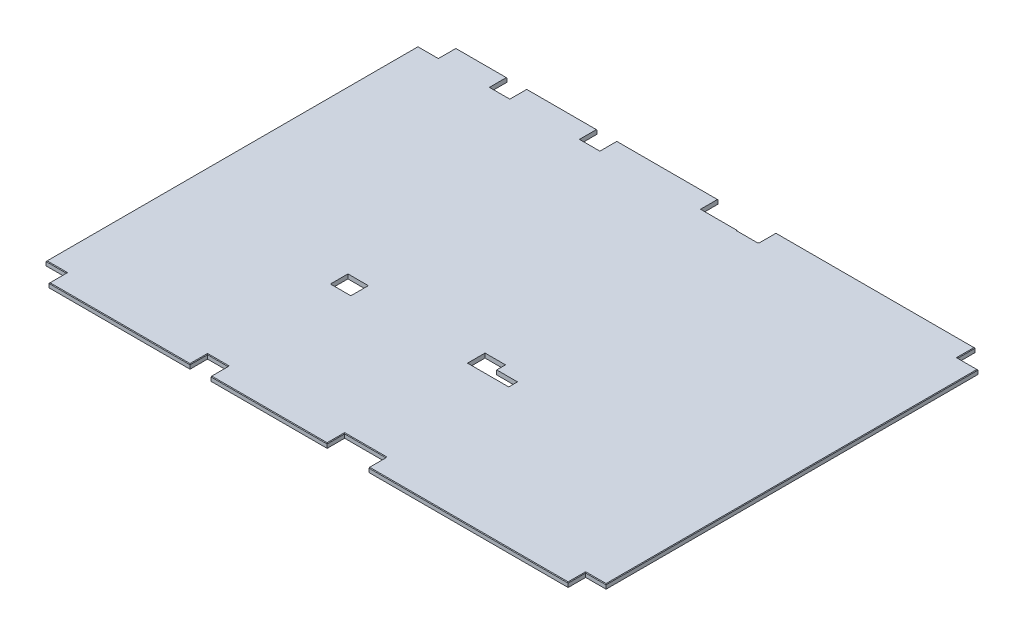
SolidWorks part; units mm, degrees
material "Oak"
ref_plane "Front Plane" through (0, 0, 0) normal (0, 0, 1) x (1, 0, 0)
ref_plane "Top Plane" through (0, 0, 0) normal (0, 1, 0) x (1, 0, 0)
ref_plane "Right Plane" through (0, 0, 0) normal (1, 0, 0) x (0, 0, -1)
sketch "Sketch1" plane through (0, 0, 0) normal (0, 1, 0) x (1, 0, 0)
  line L1 (0, 1771.65) -> (2438.4, 1771.65)
  line L2 (0, 1771.65) -> (0, 0)
  line L3 (0, 0) -> (2438.4, 0)
  line L4 (2438.4, 1771.65) -> (2438.4, 0)
  dimension "D1" = 1771.65
  dimension "D2" = 2438.4
extrude "Boss-Extrude1" add sketch "Sketch1" along normal mid plane 19.05
sketch "Sketch2" plane through (0, 9.525, 0) normal (0, 1, 0) x (1, 0, 0)
  line L0 (0, 0) -> (2438.4, 0) construction
  line L5 (2438.4, 1771.65) -> (0, 1771.65) construction
  line L6 (1390.6627, 1771.65) -> (1479.5627, 1771.65)
  line L7 (0, 1771.65) -> (88.9, 1771.65)
  line L8 (0, 1771.65) -> (0, 1695.45)
  line L9 (0, 1695.45) -> (88.9, 1695.45)
  line L10 (88.9, 1771.65) -> (88.9, 1695.45)
  line L15 (2438.4, 0) -> (2438.4, 1771.65) construction
  line L24 (2349.5, 1771.65) -> (2438.4, 1771.65)
  line L25 (2349.5, 1771.65) -> (2349.5, 1695.45)
  line L26 (2349.5, 1695.45) -> (2438.4, 1695.45)
  line L27 (2438.4, 1771.65) -> (2438.4, 1695.45)
  line L29 (0, 1771.65) -> (0, 0) construction
  line L32 (0, 885.825) -> (2438.4, 885.825) construction
  line L33 (1300.1752, 0) -> (1300.1752, 76.2)
  line L34 (1477.9752, 0) -> (1300.1752, 0)
  line L35 (792.1752, 0) -> (792.1752, 76.2)
  line L36 (2438.4, 0) -> (2438.4, 76.2)
  line L37 (2349.5, 76.2) -> (2438.4, 76.2)
  line L38 (2349.5, 0) -> (2349.5, 76.2)
  line L39 (2349.5, 0) -> (2438.4, 0)
  line L44 (1477.9752, 0) -> (1477.9752, 76.2)
  line L45 (1300.1752, 76.2) -> (1477.9752, 76.2)
  line L46 (703.2752, 76.2) -> (792.1752, 76.2)
  line L47 (703.2752, 0) -> (703.2752, 76.2)
  line L48 (703.2752, 0) -> (792.1752, 0)
  line L49 (88.9, 0) -> (88.9, 76.2)
  line L50 (0, 76.2) -> (88.9, 76.2)
  line L51 (0, 0) -> (0, 76.2)
  line L52 (0, 0) -> (88.9, 0)
  line L53 (1390.6627, 1771.65) -> (1390.6627, 1695.45)
  line L54 (1390.6627, 1695.45) -> (1479.5627, 1695.45)
  line L55 (1479.5627, 1771.65) -> (1479.5627, 1695.45)
  point P4 (1390.6627, 1733.55)
  point P25 (703.2752, 38.1)
  point P27 (792.1752, 38.1)
  point P40 (1300.1752, 38.1)
  point P54 (1479.5627, 1733.55)
  dimension "D1" = 76.2
  dimension "D2" = 88.9
  dimension "D3" = 614.3752
  dimension "D4" = 508
  dimension "D5" = 88.9
  dimension "D6" = 177.8
  dimension "D7" = 871.5248
  dimension "D8" = 2349.5
  dimension "D9" = 1390.6627
  dimension "D10" = 88.9
extrude "Cut-Extrude1" cut sketch "Sketch2" against normal through all
chamfer "Chamfer1" distance 2.54 angle 45 24 edges at (0, 9.525, -885.825) (44.45, 9.525, -1695.45) (88.9, 9.525, -1733.55) (739.7813, 9.525, -1771.65) (1914.5313, 9.525, -1771.65) (2349.5, 9.525, -1733.55) (2393.95, 9.525, -1695.45) (2438.4, 9.525, -885.825) (2393.95, 9.525, -76.2) (2349.5, 9.525, -38.1) (1913.7376, 9.525, 0) (1477.9752, 9.525, -38.1) (1389.0752, 9.525, -76.2) (1300.1752, 9.525, -38.1) (1046.1752, 9.525, 0) (792.1752, 9.525, -38.1) (747.7252, 9.525, -76.2) (703.2752, 9.525, -38.1) (396.0876, 9.525, 0) (88.9, 9.525, -38.1) (44.45, 9.525, -76.2) (1390.6627, 9.525, -1733.55) (1435.1127, 9.525, -1695.45) (1479.5627, 9.525, -1733.55)
sketch "Sketch4" plane through (0, 9.525, 0) normal (0, 1, 0) x (1, 0, 0)
  line L0 (0, 1695.45) -> (88.9, 1695.45) construction
  line L1 (311.15, 1771.65) -> (400.05, 1771.65)
  line L2 (311.15, 1771.65) -> (311.15, 1695.45)
  line L3 (311.15, 1695.45) -> (400.05, 1695.45)
  line L4 (400.05, 1771.65) -> (400.05, 1695.45)
  line L5 (1230.3252, 1771.65) -> (1319.2252, 1771.65)
  line L6 (1230.3252, 1771.65) -> (1230.3252, 1695.45)
  line L7 (1230.3252, 1695.45) -> (1319.2252, 1695.45)
  line L8 (1319.2252, 1771.65) -> (1319.2252, 1695.45)
  line L10 (88.9, 1771.65) -> (1390.6627, 1771.65) construction
  line L11 (88.9, 1771.65) -> (1390.6627, 1771.65) construction
  point P17 (311.15, 1733.55)
  point P18 (400.05, 1733.55)
  dimension "D1" = 311.15
  dimension "D2" = 88.9
  dimension "D3" = 1230.3252
  dimension "D4" = 88.9
extrude "Cut-Extrude2" cut sketch "Sketch4" against normal through all
sketch "Sketch5" plane through (0, 9.525, 0) normal (0, 1, 0) x (1, 0, 0)
  line L1 (0, 1771.65) -> (88.9, 1771.65)
  line L2 (0, 1771.65) -> (0, 1695.45)
  line L3 (0, 1695.45) -> (88.9, 1695.45)
  line L4 (88.9, 1771.65) -> (88.9, 1695.45)
  line L5 (311.15, 1771.65) -> (400.05, 1771.65)
  line L6 (311.15, 1771.65) -> (311.15, 1695.45)
  line L7 (311.15, 1695.45) -> (400.05, 1695.45)
  line L8 (400.05, 1771.65) -> (400.05, 1695.45)
  line L9 (703.3006, 1771.65) -> (792.2006, 1771.65)
  line L10 (703.3006, 1771.65) -> (703.3006, 1695.45)
  line L11 (703.3006, 1695.45) -> (792.2006, 1695.45)
  line L12 (792.2006, 1771.65) -> (792.2006, 1695.45)
  line L13 (1230.3252, 1771.65) -> (1485.0491, 1771.65)
  line L14 (1230.3252, 1771.65) -> (1230.3252, 1695.45)
  line L15 (1230.3252, 1695.45) -> (1485.0491, 1695.45)
  line L16 (1485.0491, 1771.65) -> (1485.0491, 1695.45)
  line L17 (2349.5, 1771.65) -> (2438.4, 1771.65)
  line L18 (2349.5, 1771.65) -> (2349.5, 1695.45)
  line L19 (2349.5, 1695.45) -> (2438.4, 1695.45)
  line L20 (2438.4, 1771.65) -> (2438.4, 1695.45)
  line L21 (706.4756, 684.2125) -> (795.3756, 684.2125)
  line L22 (706.4756, 684.2125) -> (706.4756, 608.0125)
  line L23 (706.4756, 608.0125) -> (795.3756, 608.0125)
  line L24 (795.3756, 684.2125) -> (795.3756, 608.0125)
  line L25 (1303.3756, 684.2252) -> (1392.3672, 684.2252)
  line L26 (1303.3756, 684.2252) -> (1303.3756, 608.0252)
  line L27 (1303.3756, 608.0252) -> (1482.7631, 608.0252)
  line L28 (1482.7631, 646.1252) -> (1482.7631, 608.0252)
  line L30 (1392.3672, 684.2252) -> (1392.3672, 646.1252)
  line L31 (1392.3672, 646.1252) -> (1482.7631, 646.1252)
  line L33 (0, 76.2) -> (88.9, 76.2)
  line L34 (0, 76.2) -> (0, 0)
  line L35 (0, 0) -> (88.9, 0)
  line L36 (88.9, 76.2) -> (88.9, 0)
  line L37 (795.3756, 0) -> (703.2752, 0)
  line L38 (795.3756, 0) -> (795.3756, 76.2)
  line L39 (795.3756, 76.2) -> (703.2752, 76.2)
  line L40 (703.2752, 0) -> (703.2752, 76.2)
  line L41 (1482.7631, 0) -> (1303.3756, 0)
  line L42 (1482.7631, 0) -> (1482.7631, 76.2)
  line L43 (1482.7631, 76.2) -> (1303.3756, 76.2)
  line L44 (1303.3756, 0) -> (1303.3756, 76.2)
  line L45 (2438.4, 0) -> (2349.5, 0)
  line L46 (2438.4, 0) -> (2438.4, 76.2)
  line L47 (2438.4, 76.2) -> (2349.5, 76.2)
  line L48 (2349.5, 0) -> (2349.5, 76.2)
extrude "Cut-Extrude3" cut sketch "Sketch5" against normal through all
